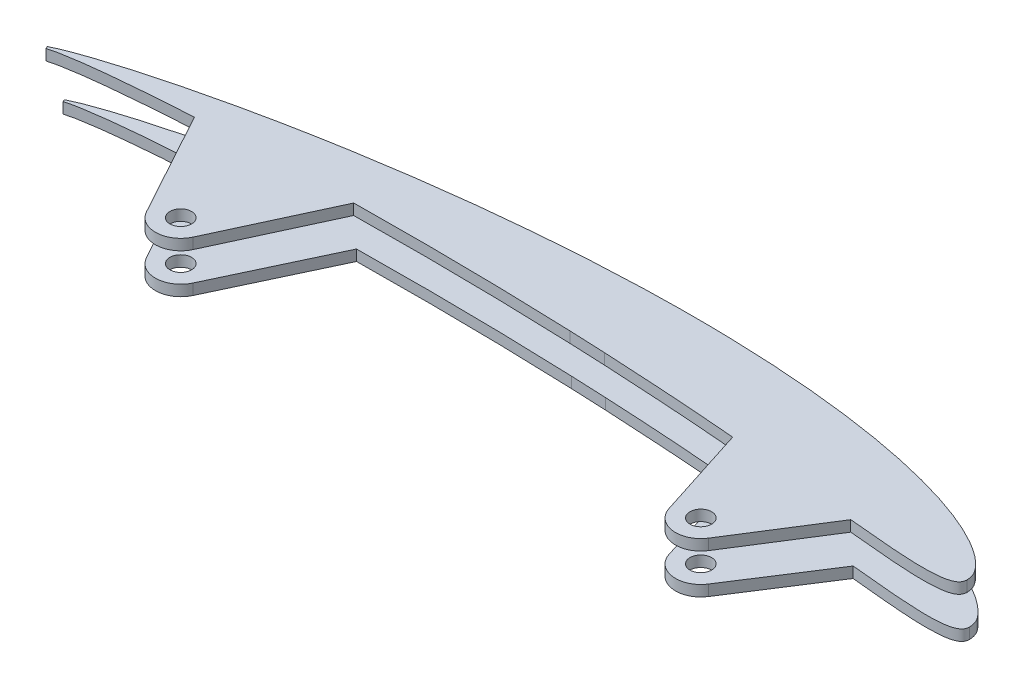
SolidWorks part; units mm, degrees
material "7075-O (SS)"
ref_plane "Płaszczyzna XY" through (0, 0, 0) normal (0, 0, 1) x (1, 0, 0)
ref_plane "Płaszczyzna XZ" through (0, 0, 0) normal (0, 1, 0) x (1, 0, 0)
ref_plane "Płaszczyzna YZ" through (0, 0, 0) normal (1, 0, 0) x (0, 0, -1)
ref_plane "Płaszczyzna1" through (0, 238, 0) normal (0, 1, 0) x (1, 0, 0)
sketch "Szkic1" plane through (0, 238, 0) normal (0, 1, 0) x (1, 0, 0)
  circle A2 centre (-158.1354, -286.7847) radius 3
  circle A3 centre (-14.2192, -286.7847) radius 3
ref_plane "Płaszczyzna2" through (0, 200, 0) normal (0, 1, 0) x (1, 0, 0)
ref_plane "Płaszczyzna3" through (0, 300, 0) normal (0, 1, 0) x (1, 0, 0)
sketch "Szkic4" plane through (0, 238, 0) normal (0, 1, 0) x (1, 0, 0)
  line L0 (-177.1875, -260.6248) -> (-177.1875, -252.322) construction
  line L1 (-217.6215, -264.2296) -> (-217.337, -264.8723) construction
  line L2 (-77.1875, -260.0525) -> (-77.1875, -239.7378) construction
  line L3 (-167.1875, -250.2215) -> (-167.1875, -260.149) construction
  line L4 (-67.1875, -239.5403) -> (-67.1875, -260.4878) construction
  line L5 (-177.1875, -260.6248) -> (-177.1875, -252.322)
  line L6 (-217.6215, -264.2296) -> (-217.337, -264.8723)
  line L7 (-77.1875, -260.0525) -> (-77.1875, -239.7378)
  line L8 (-167.1875, -250.2215) -> (-167.1875, -260.149)
  line L9 (-67.1875, -239.5403) -> (-67.1875, -260.4878)
  spline S0 degree 3 poles (-773.6134, 1654.905) (-274.1797, -356.4765) (-253.2091, -272.3692) (-214.0607, -264.0917) (-213.2291, -263.9504) (-210.7345, -263.5446) (-209.0683, -263.2987) (-205.7277, -262.8733) (-204.0539, -262.6885) (-200.7042, -262.3356) (-199.0277, -262.1712) (-193.9943, -261.7198) (-190.6354, -261.4658) (34.4232, -246.0493) (265.0376, -357.8059) (348.3541, 1627.5072) knots -2.844906 -2.844906 -2.844906 -2.844906 0.0625 0.0625 0.125 0.125 0.25 0.25 0.375 0.375 0.5 0.5 0.75 0.75 17.242593 17.242593 17.242593 17.242593 only from (-217.337, -264.8723) to (-177.1875, -260.6248) construction
  spline S1 degree 3 poles (60.8919, 1687.1509) (309.9958, -340.0916) (37.6758, -199.3325) (-190.8874, -255.5572) (-194.2966, -256.4387) (-199.379, -257.853) (-201.0678, -258.3407) (-204.4346, -259.3487) (-206.114, -259.8648) (-209.4516, -260.9614) (-211.1097, -261.5418) (-213.5829, -262.455) (-214.4037, -262.7702) (-251.5133, -278.6435) (-266.5922, -358.4286) (-952.7939, 1594.0551) knots -16.220905 -16.220905 -16.220905 -16.220905 0.25 0.25 0.5 0.5 0.625 0.625 0.75 0.75 0.875 0.875 0.9375 0.9375 3.736836 3.736836 3.736836 3.736836 only from (-177.1875, -252.322) to (-217.6215, -264.2296) construction
  spline S2 degree 3 poles (-859.0451, -2060.1905) (-789.747, -406.3492) (-467.8278, -266.0641) (-137.1883, -259.302) (-129.6874, -259.223) (-114.6863, -259.2076) (-107.1859, -259.272) (340.0464, -267.5295) (781.5772, -529.8612) (507.8935, -2007.7681) knots -10.519738 -10.519738 -10.519738 -10.519738 0.25 0.25 0.5 0.5 0.75 0.75 15.407533 15.407533 15.407533 15.407533 only from (-167.1875, -260.149) to (-77.1875, -260.0525) construction
  spline S3 degree 3 poles (853.9721, -1957.7775) (495.4873, -455.0389) (197.6283, -224.7842) (-92.3024, -240.4219) (-96.0781, -240.6686) (-107.3875, -241.5295) (-114.9069, -242.264) (-129.9087, -244.0302) (-137.3911, -245.0615) (-459.8317, -295.9333) (-748.6541, -604.9507) (174.6577, -2127.498) knots -9.344841 -9.344841 -9.344841 -9.344841 0.125 0.125 0.25 0.25 0.5 0.5 0.75 0.75 11.299772 11.299772 11.299772 11.299772 only from (-77.1875, -239.7378) to (-167.1875, -250.2215) construction
  spline S4 degree 3 poles (-865.1409, -1889.5694) (-1033.4844, -513.2432) (-522.9609, -226.7339) (-36.2052, -262.4285) (-31.7848, -262.7783) (-22.9495, -263.5384) (-18.5341, -263.943) (-9.7062, -264.7864) (-5.2939, -265.2257) (3.5302, -266.1114) (7.9423, -266.5536) (14.5648, -267.1684) (16.7732, -267.3634) (20.0893, -267.6099) (21.1954, -267.6848) (23.4083, -267.8179) (24.5152, -267.8767) (26.7306, -267.9591) (27.8392, -267.9811) (29.5016, -267.9615) (30.0559, -267.9464) (31.1633, -267.8956) (31.7163, -267.8604) (32.8201, -267.7551) (33.3703, -267.6856) (34.1854, -267.5298) (34.4554, -267.4691) (34.9915, -267.3246) (35.2566, -267.2418) (35.773, -267.0437) (36.0263, -266.9279) (36.3855, -266.7162) (36.5007, -266.6394) (36.7189, -266.4691) (36.8229, -266.3746) (37.0094, -266.1686) (37.0918, -266.0577) (37.2315, -265.818) (37.2888, -265.689) (41.071, -254.2074) (-52.4452, -211.0611) (1562.6567, -1557.5297) knots -13.382604 -13.382604 -13.382604 -13.382604 0.25 0.25 0.375 0.375 0.5 0.5 0.625 0.625 0.75 0.75 0.8125 0.8125 0.84375 0.84375 0.875 0.875 0.90625 0.90625 0.921875 0.921875 0.9375 0.9375 0.953125 0.953125 0.960937 0.960937 0.96875 0.96875 0.976562 0.976562 0.980469 0.980469 0.984375 0.984375 0.988281 0.988281 0.992187 0.992187 1.329358 1.329358 1.329358 1.329358 only from (-67.1875, -260.4878) to (37.4579, -264.735) construction
  spline S5 degree 3 poles (-1939.7052, -564.4087) (-27.7958, -308.7141) (40.4486, -281.923) (37.3336, -263.7388) (37.2775, -263.4932) (37.1338, -263.0127) (37.0456, -262.7761) (27.3678, -241.5942) (-114.9361, -287.6689) (1789.5758, 699.8944) knots -17.857179 -17.857179 -17.857179 -17.857179 0.25 0.25 0.5 0.5 0.75 0.75 23.710593 23.710593 23.710593 23.710593 only from (37.4579, -264.735) to (36.5842, -261.8859) construction
  spline S6 degree 3 poles (-1393.8742, -1658.4353) (36.4339, -313.6235) (48.8131, -275.2585) (35.1577, -260.108) (34.7547, -259.7063) (33.9206, -258.9287) (33.4869, -258.5529) (32.5999, -257.8396) (32.1462, -257.5004) (30.7594, -256.5272) (29.8012, -255.936) (27.8477, -254.8175) (26.8513, -254.2918) (24.8278, -253.2934) (23.7997, -252.8212) (21.719, -251.9228) (20.6709, -251.4982) (17.5078, -250.2833) (15.3747, -249.5507) (11.0718, -248.2012) (8.9018, -247.585) (4.5325, -246.4456) (2.3308, -245.9223) (-4.2911, -244.4747) (-8.73, -243.6707) (-17.6444, -242.306) (-22.1201, -241.7463) (-31.1017, -240.8281) (-35.6086, -240.4699) (-44.6214, -239.9288) (-49.1309, -239.7456) (-399.8232, -231.444) (-761.9096, -671.4241) (-1036.1858, 1362.7535) knots -0.529268 -0.529268 -0.529268 -0.529268 0.015625 0.015625 0.03125 0.03125 0.046875 0.046875 0.0625 0.0625 0.09375 0.09375 0.125 0.125 0.15625 0.15625 0.1875 0.1875 0.25 0.25 0.3125 0.3125 0.375 0.375 0.5 0.5 0.625 0.625 0.75 0.75 0.875 0.875 10.465149 10.465149 10.465149 10.465149 only from (36.5842, -261.8859) to (-67.1875, -239.5403) construction
  spline S7 degree 3 poles (-217.337, -264.8723) (-216.5243, -264.6494) (-215.7084, -264.4401) (-214.0607, -264.0917) (-213.2291, -263.9504) (-210.7345, -263.5446) (-209.0683, -263.2987) (-205.7277, -262.8733) (-204.0539, -262.6885) (-200.7042, -262.3356) (-199.0277, -262.1712) (-193.9943, -261.7198) (-190.6354, -261.4658) (-183.9142, -261.0054) (-180.5516, -260.8044) (-177.1875, -260.6248) knots 0 0 0 0 0.0625 0.0625 0.125 0.125 0.25 0.25 0.375 0.375 0.5 0.5 0.75 0.75 1 1 1 1
  spline S8 degree 3 poles (-177.1875, -252.322) (-180.6246, -253.0805) (-184.0527, -253.8759) (-190.8874, -255.5572) (-194.2966, -256.4387) (-199.379, -257.853) (-201.0678, -258.3407) (-204.4346, -259.3487) (-206.114, -259.8648) (-209.4516, -260.9614) (-211.1097, -261.5418) (-213.5829, -262.455) (-214.4037, -262.7702) (-216.0246, -263.4635) (-216.8245, -263.8422) (-217.6215, -264.2296) knots 0 0 0 0 0.25 0.25 0.5 0.5 0.625 0.625 0.75 0.75 0.875 0.875 0.9375 0.9375 1 1 1 1
  spline S9 degree 3 poles (-167.1875, -260.149) (-159.6908, -259.8343) (-152.1904, -259.6088) (-137.1883, -259.302) (-129.6874, -259.223) (-114.6863, -259.2076) (-107.1859, -259.272) (-92.1857, -259.5489) (-84.6851, -259.7613) (-77.1875, -260.0525) knots 0 0 0 0 0.25 0.25 0.5 0.5 0.75 0.75 1 1 1 1
  spline S10 degree 3 poles (-77.1875, -239.7378) (-80.9688, -239.8536) (-84.748, -240.0145) (-92.3024, -240.4219) (-96.0781, -240.6686) (-107.3875, -241.5295) (-114.9069, -242.264) (-129.9087, -244.0302) (-137.3911, -245.0615) (-152.3192, -247.4167) (-159.7686, -248.74) (-167.1875, -250.2215) knots 0 0 0 0 0.125 0.125 0.25 0.25 0.5 0.5 0.75 0.75 1 1 1 1
  spline S11 degree 3 poles (-67.1875, -260.4878) (-58.3277, -260.9152) (-49.473, -261.4556) (-36.2052, -262.4285) (-31.7848, -262.7783) (-22.9495, -263.5384) (-18.5341, -263.943) (-9.7062, -264.7864) (-5.2939, -265.2257) (3.5302, -266.1114) (7.9423, -266.5536) (14.5648, -267.1684) (16.7732, -267.3634) (20.0893, -267.6099) (21.1954, -267.6848) (23.4083, -267.8179) (24.5152, -267.8767) (26.7306, -267.9591) (27.8392, -267.9811) (29.5016, -267.9615) (30.0559, -267.9464) (31.1633, -267.8956) (31.7163, -267.8604) (32.8201, -267.7551) (33.3703, -267.6856) (34.1854, -267.5298) (34.4554, -267.4691) (34.9915, -267.3246) (35.2566, -267.2418) (35.773, -267.0437) (36.0263, -266.9279) (36.3855, -266.7162) (36.5007, -266.6394) (36.7189, -266.4691) (36.8229, -266.3746) (37.0094, -266.1686) (37.0918, -266.0577) (37.2315, -265.818) (37.2888, -265.689) (37.4188, -265.2945) (37.4532, -265.0144) (37.4579, -264.735) knots 0 0 0 0 0.25 0.25 0.375 0.375 0.5 0.5 0.625 0.625 0.75 0.75 0.8125 0.8125 0.84375 0.84375 0.875 0.875 0.90625 0.90625 0.921875 0.921875 0.9375 0.9375 0.953125 0.953125 0.960937 0.960937 0.96875 0.96875 0.976562 0.976562 0.980469 0.980469 0.984375 0.984375 0.988281 0.988281 0.992187 0.992187 1 1 1 1
  spline S12 degree 3 poles (37.4579, -264.735) (37.4473, -264.4834) (37.4185, -264.2341) (37.3336, -263.7388) (37.2775, -263.4932) (37.1338, -263.0127) (37.0456, -262.7761) (36.8371, -262.3198) (36.7171, -262.0996) (36.5842, -261.8859) knots 0 0 0 0 0.25 0.25 0.5 0.5 0.75 0.75 1 1 1 1
  spline S13 degree 3 poles (36.5842, -261.8859) (36.2786, -261.3945) (35.919, -260.9527) (35.1577, -260.108) (34.7547, -259.7063) (33.9206, -258.9287) (33.4869, -258.5529) (32.5999, -257.8396) (32.1462, -257.5004) (30.7594, -256.5272) (29.8012, -255.936) (27.8477, -254.8175) (26.8513, -254.2918) (24.8278, -253.2934) (23.7997, -252.8212) (21.719, -251.9228) (20.6709, -251.4982) (17.5078, -250.2833) (15.3747, -249.5507) (11.0718, -248.2012) (8.9018, -247.585) (4.5325, -246.4456) (2.3308, -245.9223) (-4.2911, -244.4747) (-8.73, -243.6707) (-17.6444, -242.306) (-22.1201, -241.7463) (-31.1017, -240.8281) (-35.6086, -240.4699) (-44.6214, -239.9288) (-49.1309, -239.7456) (-58.1552, -239.5319) (-62.6701, -239.5013) (-67.1875, -239.5403) knots 0 0 0 0 0.015625 0.015625 0.03125 0.03125 0.046875 0.046875 0.0625 0.0625 0.09375 0.09375 0.125 0.125 0.15625 0.15625 0.1875 0.1875 0.25 0.25 0.3125 0.3125 0.375 0.375 0.5 0.5 0.625 0.625 0.75 0.75 0.875 0.875 1 1 1 1
sketch "Szkic5" plane through (0, 238, 0) normal (0, 1, 0) x (1, 0, 0)
  line L0 (-217.6215, -264.2296) -> (-217.337, -264.8723) construction
  line L1 (-217.6215, -264.2296) -> (-217.337, -264.8723)
  line L2 (-67.1875, -260.4878) -> (-77.1875, -260.0525)
  line L3 (-67.1875, -239.5403) -> (-77.1875, -239.7378)
  line L5 (-167.1875, -250.2215) -> (-177.1875, -252.322)
  line L6 (-8.3043, -290.5282) -> (6.9373, -266.4461)
  line L7 (-20.8858, -288.9192) -> (-29.1835, -263.0038)
  line L8 (-151.7818, -289.7228) -> (-137.7289, -259.3343)
  line L9 (-164.2765, -290.1442) -> (-180.3299, -260.7991)
  circle A0 centre (-14.2192, -286.7847) radius 3
  circle A1 centre (-158.1354, -286.7847) radius 3
  arc A2 (-20.8858, -288.9192) -> (-8.3043, -290.5282) centre (-14.2192, -286.7847) ccw
  arc A3 (-164.2765, -290.1442) -> (-151.7818, -289.7228) centre (-158.1354, -286.7847) ccw
  spline S1 degree 3 poles (60.8919, 1687.1509) (309.9958, -340.0916) (37.6758, -199.3325) (-190.8874, -255.5572) (-194.2966, -256.4387) (-199.379, -257.853) (-201.0678, -258.3407) (-204.4346, -259.3487) (-206.114, -259.8648) (-209.4516, -260.9614) (-211.1097, -261.5418) (-213.5829, -262.455) (-214.4037, -262.7702) (-251.5133, -278.6435) (-266.5922, -358.4286) (-952.7939, 1594.0551) knots -16.220905 -16.220905 -16.220905 -16.220905 0.25 0.25 0.5 0.5 0.625 0.625 0.75 0.75 0.875 0.875 0.9375 0.9375 3.736836 3.736836 3.736836 3.736836 only from (-177.1875, -252.322) to (-217.6215, -264.2296) construction
  spline S3 degree 3 poles (853.9721, -1957.7775) (495.4873, -455.0389) (197.6283, -224.7842) (-92.3024, -240.4219) (-96.0781, -240.6686) (-107.3875, -241.5295) (-114.9069, -242.264) (-129.9087, -244.0302) (-137.3911, -245.0615) (-459.8317, -295.9333) (-748.6541, -604.9507) (174.6577, -2127.498) knots -9.344841 -9.344841 -9.344841 -9.344841 0.125 0.125 0.25 0.25 0.5 0.5 0.75 0.75 11.299772 11.299772 11.299772 11.299772 only from (-77.1875, -239.7378) to (-167.1875, -250.2215) construction
  spline S4 degree 3 poles (-1939.7052, -564.4087) (-27.7958, -308.7141) (40.4486, -281.923) (37.3336, -263.7388) (37.2775, -263.4932) (37.1338, -263.0127) (37.0456, -262.7761) (27.3678, -241.5942) (-114.9361, -287.6689) (1789.5758, 699.8944) knots -17.857179 -17.857179 -17.857179 -17.857179 0.25 0.25 0.5 0.5 0.75 0.75 23.710593 23.710593 23.710593 23.710593 only from (37.4579, -264.735) to (36.5842, -261.8859) construction
  spline S5 degree 3 poles (-1393.8742, -1658.4353) (36.4339, -313.6235) (48.8131, -275.2585) (35.1577, -260.108) (34.7547, -259.7063) (33.9206, -258.9287) (33.4869, -258.5529) (32.5999, -257.8396) (32.1462, -257.5004) (30.7594, -256.5272) (29.8012, -255.936) (27.8477, -254.8175) (26.8513, -254.2918) (24.8278, -253.2934) (23.7997, -252.8212) (21.719, -251.9228) (20.6709, -251.4982) (17.5078, -250.2833) (15.3747, -249.5507) (11.0718, -248.2012) (8.9018, -247.585) (4.5325, -246.4456) (2.3308, -245.9223) (-4.2911, -244.4747) (-8.73, -243.6707) (-17.6444, -242.306) (-22.1201, -241.7463) (-31.1017, -240.8281) (-35.6086, -240.4699) (-44.6214, -239.9288) (-49.1309, -239.7456) (-399.8232, -231.444) (-761.9096, -671.4241) (-1036.1858, 1362.7535) knots -0.529268 -0.529268 -0.529268 -0.529268 0.015625 0.015625 0.03125 0.03125 0.046875 0.046875 0.0625 0.0625 0.09375 0.09375 0.125 0.125 0.15625 0.15625 0.1875 0.1875 0.25 0.25 0.3125 0.3125 0.375 0.375 0.5 0.5 0.625 0.625 0.75 0.75 0.875 0.875 10.465149 10.465149 10.465149 10.465149 only from (36.5842, -261.8859) to (-67.1875, -239.5403) construction
  spline S7 degree 3 poles (-217.337, -264.8723) (-216.5243, -264.6494) (-215.7084, -264.4401) (-214.0607, -264.0917) (-213.2291, -263.9504) (-210.7345, -263.5446) (-209.0683, -263.2987) (-205.7277, -262.8733) (-204.0539, -262.6885) (-200.7042, -262.3356) (-199.0277, -262.1712) (-193.9943, -261.7198) (-190.6354, -261.4658) (-184.9607, -261.0771) (-182.6457, -260.9324) (-180.3299, -260.7991) knots 0 0 0 0 0.0625 0.0625 0.125 0.125 0.25 0.25 0.375 0.375 0.5 0.5 0.75 0.75 0.922147 0.922147 0.922147 0.922147
  spline S8 degree 3 poles (-177.1875, -252.322) (-180.6246, -253.0805) (-184.0527, -253.8759) (-190.8874, -255.5572) (-194.2966, -256.4387) (-199.379, -257.853) (-201.0678, -258.3407) (-204.4346, -259.3487) (-206.114, -259.8648) (-209.4516, -260.9614) (-211.1097, -261.5418) (-213.5829, -262.455) (-214.4037, -262.7702) (-216.0246, -263.4635) (-216.8245, -263.8422) (-217.6215, -264.2296) knots 0 0 0 0 0.25 0.25 0.5 0.5 0.625 0.625 0.75 0.75 0.875 0.875 0.9375 0.9375 1 1 1 1
  spline S9 degree 3 poles (-137.7289, -259.3343) (-132.5481, -259.26) (-127.3674, -259.2206) (-114.6863, -259.2076) (-107.1859, -259.272) (-92.1857, -259.5489) (-84.6851, -259.7613) (-77.1875, -260.0525) knots 0.327328 0.327328 0.327328 0.327328 0.5 0.5 0.75 0.75 1 1 1 1
  spline S10 degree 3 poles (-77.1875, -239.7378) (-80.9688, -239.8536) (-84.748, -240.0145) (-92.3024, -240.4219) (-96.0781, -240.6686) (-107.3875, -241.5295) (-114.9069, -242.264) (-129.9087, -244.0302) (-137.3911, -245.0615) (-152.3192, -247.4167) (-159.7686, -248.74) (-167.1875, -250.2215) knots 0 0 0 0 0.125 0.125 0.25 0.25 0.5 0.5 0.75 0.75 1 1 1 1
  spline S11 degree 3 poles (37.4579, -264.735) (37.4473, -264.4834) (37.4185, -264.2341) (37.3336, -263.7388) (37.2775, -263.4932) (37.1338, -263.0127) (37.0456, -262.7761) (36.8371, -262.3198) (36.7171, -262.0996) (36.5842, -261.8859) knots 0 0 0 0 0.25 0.25 0.5 0.5 0.75 0.75 1 1 1 1
  spline S12 degree 3 poles (36.5842, -261.8859) (36.2786, -261.3945) (35.919, -260.9527) (35.1577, -260.108) (34.7547, -259.7063) (33.9206, -258.9287) (33.4869, -258.5529) (32.5999, -257.8396) (32.1462, -257.5004) (30.7594, -256.5272) (29.8012, -255.936) (27.8477, -254.8175) (26.8513, -254.2918) (24.8278, -253.2934) (23.7997, -252.8212) (21.719, -251.9228) (20.6709, -251.4982) (17.5078, -250.2833) (15.3747, -249.5507) (11.0718, -248.2012) (8.9018, -247.585) (4.5325, -246.4456) (2.3308, -245.9223) (-4.2911, -244.4747) (-8.73, -243.6707) (-17.6444, -242.306) (-22.1201, -241.7463) (-31.1017, -240.8281) (-35.6086, -240.4699) (-44.6214, -239.9288) (-49.1309, -239.7456) (-58.1552, -239.5319) (-62.6701, -239.5013) (-67.1875, -239.5403) knots 0 0 0 0 0.015625 0.015625 0.03125 0.03125 0.046875 0.046875 0.0625 0.0625 0.09375 0.09375 0.125 0.125 0.15625 0.15625 0.1875 0.1875 0.25 0.25 0.3125 0.3125 0.375 0.375 0.5 0.5 0.625 0.625 0.75 0.75 0.875 0.875 1 1 1 1
  spline S13 degree 3 poles (-67.1875, -260.4878) (-58.3277, -260.9152) (-49.473, -261.4556) (-36.8112, -262.3841) (-32.9964, -262.6829) (-29.1835, -263.0038) knots 0 0 0 0 0.25 0.25 0.35787 0.35787 0.35787 0.35787
  spline S14 degree 3 poles (6.9373, -266.4461) (8.7436, -266.6225) (10.5502, -266.7957) (14.5648, -267.1684) (16.7732, -267.3634) (20.0893, -267.6099) (21.1954, -267.6848) (23.4083, -267.8179) (24.5152, -267.8767) (26.7306, -267.9591) (27.8392, -267.9811) (29.5016, -267.9615) (30.0559, -267.9464) (31.1633, -267.8956) (31.7163, -267.8604) (32.8201, -267.7551) (33.3703, -267.6856) (34.1854, -267.5298) (34.4554, -267.4691) (34.9915, -267.3246) (35.2566, -267.2418) (35.773, -267.0437) (36.0263, -266.9279) (36.3855, -266.7162) (36.5007, -266.6394) (36.7189, -266.4691) (36.8229, -266.3746) (37.0094, -266.1686) (37.0918, -266.0577) (37.2315, -265.818) (37.2888, -265.689) (37.4188, -265.2945) (37.4532, -265.0144) (37.4579, -264.735) knots 0.698836 0.698836 0.698836 0.698836 0.75 0.75 0.8125 0.8125 0.84375 0.84375 0.875 0.875 0.90625 0.90625 0.921875 0.921875 0.9375 0.9375 0.953125 0.953125 0.960937 0.960937 0.96875 0.96875 0.976562 0.976562 0.980469 0.980469 0.984375 0.984375 0.988281 0.988281 0.992187 0.992187 1 1 1 1
  dimension "D1" = 14
  dimension "D2" = 14
extrude "Dodanie-wyciągnięcie1" add sketch "Szkic5" along normal blind 3
sketch "Szkic6" plane through (0, 230, 0) normal (0, -1, 0) x (1, 0, 0)
  line L0 (-213.2314, 264.2353) -> (-213.5117, 263.601) construction
  line L1 (-20.8915, 288.9014) -> (-29.2158, 262.6626)
  line L2 (-8.337, 290.5793) -> (7.3747, 266.2236)
  line L3 (-151.8009, 289.7637) -> (-137.3202, 258.9728)
  line L4 (-164.2646, 290.1658) -> (-180.6166, 260.5228)
  line L5 (-213.2314, 264.2353) -> (-213.5117, 263.601)
  line L10 (-77.1002, 259.6916) -> (-67.1875, 260.1258)
  line L11 (-67.1875, 239.6375) -> (-77.1002, 239.858)
  line L13 (-167.1875, 250.6154) -> (-177.1875, 252.7651)
  circle A0 centre (-14.2192, 286.7847) radius 3
  circle A1 centre (-158.1354, 286.7847) radius 3
  arc A2 (-151.8009, 289.7637) -> (-164.2646, 290.1658) centre (-158.1354, 286.7847) ccw
  arc A3 (-8.337, 290.5793) -> (-20.8915, 288.9014) centre (-14.2192, 286.7847) ccw
  spline S1 degree 3 poles (-985.7852, -1580.0272) (-260.9244, 350.6052) (-246.382, 277.7087) (-210.6232, 262.2908) (-209.8871, 262.0028) (-208.4059, 261.452) (-207.662, 261.186) (-206.1714, 260.6617) (-205.424, 260.4054) (-203.1747, 259.6569) (-201.6652, 259.1858) (-198.636, 258.2725) (-197.1168, 257.828) (-192.5491, 256.5369) (-189.4896, 255.7322) (90.4226, 185.6281) (443.9891, 416.569) (215.7586, -1629.5125) knots -2.948778 -2.948778 -2.948778 -2.948778 0.0625 0.0625 0.125 0.125 0.1875 0.1875 0.25 0.25 0.375 0.375 0.5 0.5 0.75 0.75 23.303845 23.303845 23.303845 23.303845 only from (-213.5117, 263.601) to (-177.1875, 252.7651) construction
  spline S3 degree 3 poles (-639.034, 2148.2468) (-659.2603, 550.4203) (-426.7605, 297.7047) (-152.3046, 247.7858) (-148.5705, 247.1466) (-137.3582, 245.3417) (-129.8666, 244.2877) (-114.8499, 242.4793) (-107.3248, 241.725) (-96.01, 240.8356) (-92.2339, 240.5795) (197.6491, 224.2352) (510.4203, 453.7374) (-794.9865, 2029.9072) knots -8.956774 -8.956774 -8.956774 -8.956774 0.125 0.125 0.25 0.25 0.5 0.5 0.75 0.75 0.875 0.875 10.333811 10.333811 10.333811 10.333811 only from (-167.1875, 250.6154) to (-77.1002, 239.858) construction
  spline S5 degree 3 poles (-1061.0778, -1356.6293) (-737.5519, 658.2974) (-393.7548, 232.4785) (-49.0104, 239.7985) (-44.4687, 239.9721) (-35.4018, 240.4951) (-30.8751, 240.8444) (-24.0968, 241.5217) (-21.8393, 241.7733) (-17.3287, 242.3328) (-15.0758, 242.6409) (-8.3374, 243.6579) (-3.868, 244.4583) (2.7911, 245.9) (5.0045, 246.4214) (9.4077, 247.5601) (11.5943, 248.1764) (15.9301, 249.527) (18.0794, 250.2607) (21.2661, 251.4781) (22.323, 251.9041) (24.4102, 252.8005) (25.4414, 253.2716) (27.4738, 254.2694) (28.4753, 254.7957) (30.4412, 255.9166) (31.4066, 256.5097) (32.8069, 257.4878) (33.2663, 257.83) (34.1611, 258.548) (34.5931, 258.9218) (35.4267, 259.699) (35.8297, 260.101) (49.2804, 275.0352) (38.2512, 312.8805) (-1359.2399, 1693.1991) knots -9.233922 -9.233922 -9.233922 -9.233922 0.125 0.125 0.25 0.25 0.375 0.375 0.4375 0.4375 0.5 0.5 0.625 0.625 0.6875 0.6875 0.75 0.75 0.8125 0.8125 0.84375 0.84375 0.875 0.875 0.90625 0.90625 0.9375 0.9375 0.953125 0.953125 0.96875 0.96875 0.984375 0.984375 1.52019 1.52019 1.52019 1.52019 only from (-67.1875, 239.6375) to (37.2589, 261.8859) construction
  spline S6 degree 3 poles (1784.5999, -710.1567) (-110.9817, 287.9561) (28.258, 241.9218) (37.7108, 262.7637) (37.7968, 262.9964) (37.9369, 263.4695) (37.9915, 263.7116) (41.012, 281.6417) (-26.3418, 308.4653) (-1937.3544, 574.8001) knots -22.653518 -22.653518 -22.653518 -22.653518 0.25 0.25 0.5 0.5 0.75 0.75 18.906429 18.906429 18.906429 18.906429 only from (37.2589, 261.8859) to (38.111, 264.6915) construction
  spline S7 degree 3 poles (-180.6166, 260.5228) (-182.4933, 260.6384) (-184.3694, 260.7624) (-189.2622, 261.1098) (-192.2779, 261.3457) (-196.7963, 261.7679) (-198.3014, 261.9196) (-201.3084, 262.2411) (-202.8104, 262.4122) (-205.0575, 262.7087) (-205.8054, 262.8148) (-207.2997, 263.0373) (-208.0463, 263.1525) (-209.5373, 263.3978) (-210.2815, 263.5287) (-211.7615, 263.8479) (-212.4972, 264.0362) (-213.2314, 264.2353) knots 0.094622 0.094622 0.094622 0.094622 0.25 0.25 0.5 0.5 0.625 0.625 0.75 0.75 0.8125 0.8125 0.875 0.875 0.9375 0.9375 1 1 1 1
  spline S8 degree 3 poles (-213.5117, 263.601) (-212.7957, 263.2562) (-212.0774, 262.9178) (-210.6232, 262.2908) (-209.8871, 262.0028) (-208.4059, 261.452) (-207.662, 261.186) (-206.1714, 260.6617) (-205.424, 260.4054) (-203.1747, 259.6569) (-201.6652, 259.1858) (-198.636, 258.2725) (-197.1168, 257.828) (-192.5491, 256.5369) (-189.4896, 255.7322) (-183.3523, 254.1951) (-180.2741, 253.4634) (-177.1875, 252.7651) knots 0 0 0 0 0.0625 0.0625 0.125 0.125 0.1875 0.1875 0.25 0.25 0.375 0.375 0.5 0.5 0.75 0.75 1 1 1 1
  spline S9 degree 3 poles (-77.1002, 259.6916) (-92.1099, 259.105) (-107.1311, 258.8339) (-127.2048, 258.8597) (-132.2626, 258.8992) (-137.3202, 258.9728) knots 0 0 0 0 0.5 0.5 0.668422 0.668422 0.668422 0.668422
  spline S10 degree 3 poles (-167.1875, 250.6154) (-163.4762, 249.8576) (-159.7572, 249.1413) (-152.3046, 247.7858) (-148.5705, 247.1466) (-137.3582, 245.3417) (-129.8666, 244.2877) (-114.8499, 242.4793) (-107.3248, 241.725) (-96.01, 240.8356) (-92.2339, 240.5795) (-84.6721, 240.1532) (-80.8866, 239.9829) (-77.1002, 239.858) knots 0 0 0 0 0.125 0.125 0.25 0.25 0.5 0.5 0.75 0.75 0.875 0.875 1 1 1 1
  spline S11 degree 3 poles (38.111, 264.6915) (38.1055, 264.975) (38.0702, 265.2529) (37.9325, 265.6536) (37.8717, 265.7843) (37.7246, 266.0244) (37.6373, 266.1363) (37.3419, 266.4455) (37.1118, 266.6079) (36.6155, 266.885) (36.3579, 266.9963) (35.8321, 267.1868) (35.5638, 267.2659) (35.0203, 267.4035) (34.7439, 267.4612) (33.9144, 267.6075) (33.36, 267.6707) (32.2503, 267.7652) (31.6948, 267.7959) (30.5831, 267.8382) (30.0269, 267.8492) (28.3573, 267.8562) (27.243, 267.8261) (25.0131, 267.7298) (23.8994, 267.6653) (21.6735, 267.5213) (20.5614, 267.4409) (17.227, 267.1776) (15.0069, 266.9719) (10.9828, 266.5844) (9.1786, 266.4055) (7.3747, 266.2236) knots 0 0 0 0 0.007812 0.007812 0.011719 0.011719 0.015625 0.015625 0.023437 0.023437 0.03125 0.03125 0.039062 0.039062 0.046875 0.046875 0.0625 0.0625 0.078125 0.078125 0.09375 0.09375 0.125 0.125 0.15625 0.15625 0.1875 0.1875 0.25 0.25 0.300819 0.300819 0.300819 0.300819
  spline S12 degree 3 poles (-67.1875, 239.6375) (-62.6425, 239.5863) (-58.098, 239.6056) (-49.0104, 239.7985) (-44.4687, 239.9721) (-35.4018, 240.4951) (-30.8751, 240.8444) (-24.0968, 241.5217) (-21.8393, 241.7733) (-17.3287, 242.3328) (-15.0758, 242.6409) (-8.3374, 243.6579) (-3.868, 244.4583) (2.7911, 245.9) (5.0045, 246.4214) (9.4077, 247.5601) (11.5943, 248.1764) (15.9301, 249.527) (18.0794, 250.2607) (21.2661, 251.4781) (22.323, 251.9041) (24.4102, 252.8005) (25.4414, 253.2716) (27.4738, 254.2694) (28.4753, 254.7957) (30.4412, 255.9166) (31.4066, 256.5097) (32.8069, 257.4878) (33.2663, 257.83) (34.1611, 258.548) (34.5931, 258.9218) (35.4267, 259.699) (35.8297, 260.101) (36.5919, 260.9474) (36.9526, 261.3904) (37.2589, 261.8859) knots 0 0 0 0 0.125 0.125 0.25 0.25 0.375 0.375 0.4375 0.4375 0.5 0.5 0.625 0.625 0.6875 0.6875 0.75 0.75 0.8125 0.8125 0.84375 0.84375 0.875 0.875 0.90625 0.90625 0.9375 0.9375 0.953125 0.953125 0.96875 0.96875 0.984375 0.984375 1 1 1 1
  spline S13 degree 3 poles (37.2589, 261.8859) (37.3891, 262.0965) (37.5067, 262.3136) (37.7108, 262.7637) (37.7968, 262.9964) (37.9369, 263.4695) (37.9915, 263.7116) (38.0735, 264.1987) (38.1012, 264.4439) (38.111, 264.6915) knots 0 0 0 0 0.25 0.25 0.5 0.5 0.75 0.75 1 1 1 1
  spline S14 degree 3 poles (-29.2158, 262.6626) (-32.9708, 262.3432) (-36.7275, 262.0458) (-49.3775, 261.1063) (-58.2781, 260.5583) (-67.1875, 260.1258) knots 0.644341 0.644341 0.644341 0.644341 0.75 0.75 1 1 1 1
extrude "Dodanie-wyciągnięcie2" add sketch "Szkic6" along normal blind 3 separate body
